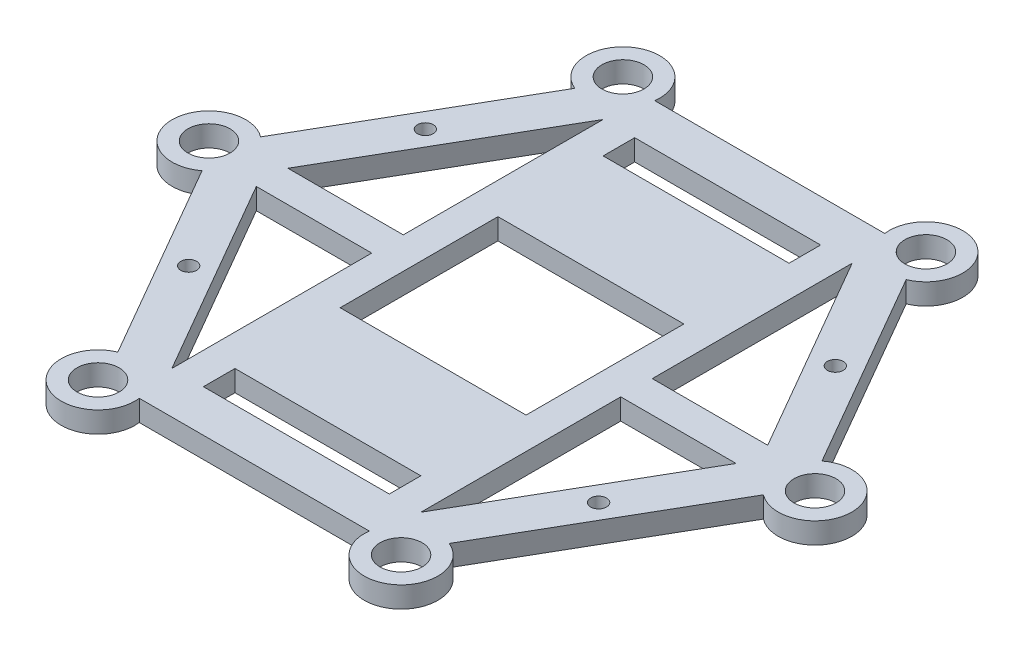
SolidWorks part; units mm, degrees
material "ABS PC"
ref_plane "前视基准面" through (0, 0, 0) normal (0, 0, 1) x (1, 0, 0)
ref_plane "上视基准面" through (0, 0, 0) normal (0, 1, 0) x (1, 0, 0)
ref_plane "右视基准面" through (0, 0, 0) normal (1, 0, 0) x (0, 0, -1)
other "Configuration Table"
sketch "草图1" plane through (0, 0, 0) normal (0, 1, 0) x (1, 0, 0)
  line L0 (-28.2902, 49) -> (-56.5803, 0)
  line L1 (-25.9808, 45) -> (-51.9615, 0) construction
  line L2 (-51.9615, 0) -> (-25.9808, -45) construction
  line L3 (-25.9808, -45) -> (25.9808, -45) construction
  line L4 (25.9808, -45) -> (51.9615, 0) construction
  line L5 (51.9615, 0) -> (25.9808, 45) construction
  line L6 (25.9808, 45) -> (-25.9808, 45) construction
  line L7 (-56.5803, 0) -> (-28.2902, -49)
  line L8 (-28.2902, -49) -> (28.2902, -49)
  line L9 (28.2902, -49) -> (56.5803, 0)
  line L10 (56.5803, 0) -> (28.2902, 49)
  line L11 (28.2902, 49) -> (-28.2902, 49)
  line L12 (-23.6714, 41) -> (-47.3427, 0)
  line L13 (-47.3427, 0) -> (-23.6714, -41)
  line L14 (-23.6714, -41) -> (23.6714, -41)
  line L15 (23.6714, -41) -> (47.3427, 0)
  line L16 (47.3427, 0) -> (23.6714, 41)
  line L17 (23.6714, 41) -> (-23.6714, 41)
  line L18 (-25.9808, 45) -> (-28.8058, 49.893) construction
  line L19 (-51.9615, 0) -> (-57.6115, 0) construction
  line L20 (-47.3427, 0) -> (47.3427, 0) construction
  line L21 (0, 41) -> (0, -41) construction
  line L22 (-17.6714, 41) -> (-17.6714, -41)
  line L23 (-23.6714, 41) -> (-23.6714, -41)
  line L24 (17.6714, 41) -> (17.6714, -41)
  line L25 (23.6714, 41) -> (23.6714, -41)
  line L26 (-23.6714, 3) -> (-45.6107, 3)
  line L27 (-23.6714, -3) -> (-45.6107, -3)
  line L28 (-17.6714, 35) -> (17.6714, 35)
  line L29 (-17.6714, 15) -> (17.6714, 15)
  line L30 (-17.6714, -15) -> (17.6714, -15)
  line L31 (-17.6714, -35) -> (17.6714, -35)
  line L32 (23.6714, -3) -> (45.6107, -3)
  line L33 (23.6714, 3) -> (45.6107, 3)
  circle A0 centre (0, 0) radius 45 construction
  circle A1 centre (-28.8058, 49.893) radius 7
  circle A2 centre (-57.6115, 0) radius 7
  circle A3 centre (-28.8058, 49.893) radius 4
  circle A4 centre (-57.6115, 0) radius 4
  circle A5 centre (-28.8058, -49.893) radius 7
  circle A6 centre (-28.8058, -49.893) radius 4
  circle A7 centre (28.8058, -49.893) radius 7
  circle A8 centre (28.8058, -49.893) radius 4
  circle A9 centre (57.6115, 0) radius 7
  circle A10 centre (57.6115, 0) radius 4
  circle A11 centre (28.8058, 49.893) radius 7
  circle A12 centre (28.8058, 49.893) radius 4
  circle A13 centre (-38.9711, 22.5) radius 1.5
  circle A14 centre (-38.9711, -22.5) radius 1.5
  circle A15 centre (38.9711, -22.5) radius 1.5
  circle A16 centre (38.9711, 22.5) radius 1.5
  dimension "D1" = 90
  dimension "D5" = 14
  dimension "D7" = 14
  dimension "D8" = 8
  dimension "D9" = 8
  dimension "D10" = 3
  dimension "D4" = 5.65
  dimension "D6" = 5.65
  dimension "D11" = 6
  dimension "D12" = 6
  dimension "D13" = 15
  dimension "D14" = 20
  dimension "D2" = 4
  dimension "D3" = 4
extrude "凸台-拉伸1" add sketch "草图1" along normal blind 4 contours A4 L0 A2 L7 | A4 L7 A2 L0 | L8 A6 L7 A5 | L7 A6 L8 A5 | A3 L0 A1 L11 | A3 L11 A1 L0 | L10 A12 L11 A11 | L11 A12 L10 A11 | L9 A10 L10 A9 | L10 A10 L9 A9 | A8 L9 A7 L8 | A8 L8 A7 L9 | L10 A11 L11 A1 L0 A2 L7 A5 L8 A7 L9 A9 A14 A13 L17 L16 L15 L14 L13 L12 A15 A16 | L27 L23 L26 L12 L13 | L17 L23 L14 L22 | L22 L29 L24 L28 | L22 L31 L24 L30 | L25 L17 L24 L14 | L33 L25 L32 L15 L16
sketch "草图2" plane through (0, 4, 0) normal (0, 1, 0) x (1, 0, 0)
  line L0 (0, 15) -> (0, 35) construction
  line L1 (-17.6714, 15) -> (17.6714, 15) construction
  line L2 (-17.6714, 35) -> (17.6714, 35) construction
  line L3 (-22.4975, 0.0037) -> (22.4772, -0.0081) construction
  line L4 (-22.5073, -37.4837) -> (-22.4877, 37.4911) construction
  line L5 (22.487, 37.4793) -> (22.4674, -37.4955) construction
  circle A0 centre (0, 25) radius 7
  circle A1 centre (-0.0131, -25.0044) radius 7
  dimension "D1" = 14
extrude "切除-拉伸1" cut sketch "草图2" along normal blind 1.1 from offset 2
